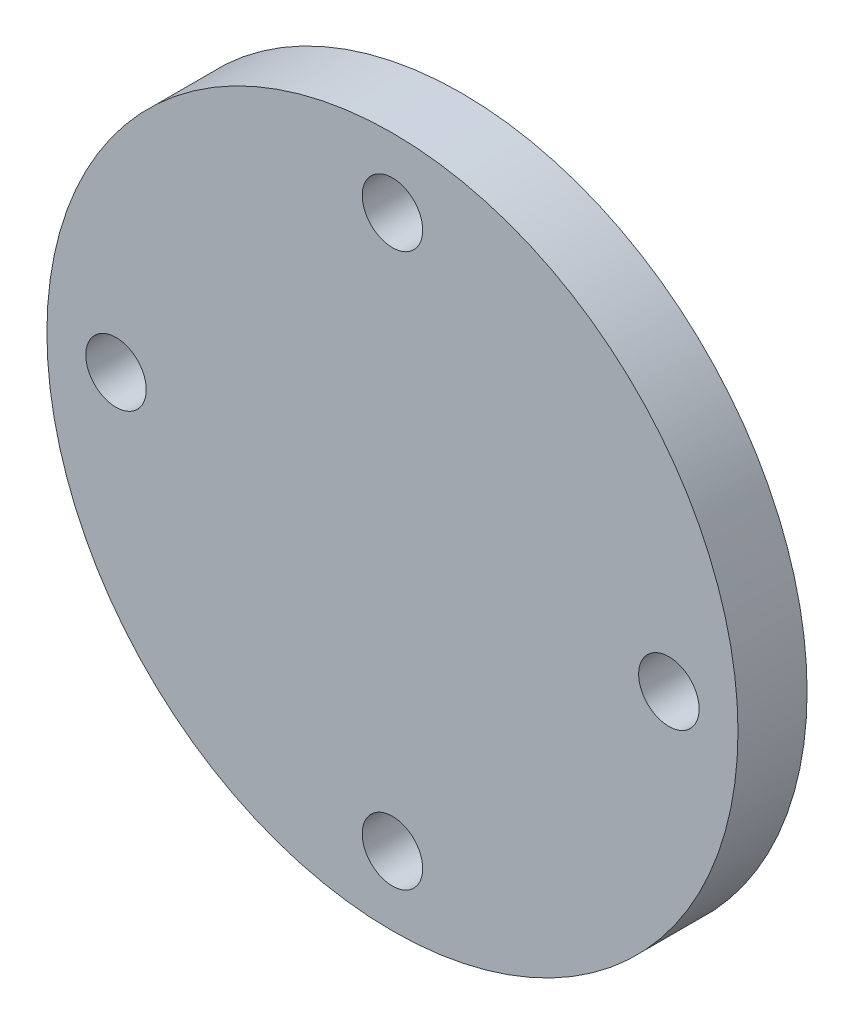
SolidWorks part; units mm, degrees
material "Cast Carbon Steel"
ref_plane "Front Plane" through (0, 0, 0) normal (0, 0, 1) x (1, 0, 0)
ref_plane "Top Plane" through (0, 0, 0) normal (0, 1, 0) x (1, 0, 0)
ref_plane "Right Plane" through (0, 0, 0) normal (1, 0, 0) x (0, 0, -1)
sketch "Sketch1" plane through (0, 0, 0) normal (0, 0, 1) x (1, 0, 0)
  circle A0 centre (0, 0) radius 63.5
  circle A2 centre (-50.8, 0) radius 5.5562
  circle A3 centre (0, 50.8) radius 5.5562
  circle A4 centre (50.8, 0) radius 5.5562
  circle A5 centre (0, -50.8) radius 5.5562
  point P15 (0, 0)
  dimension "D1" = 127
  dimension "D2" = 50.8
  dimension "D3" = 11.1125
  dimension "D4" = 4
extrude "Boss-Extrude1" add sketch "Sketch1" along normal blind 12.7
sketch "Sketch2" plane through (0, 0, 0) normal (0, 0, -1) x (-1, 0, 0)
  line L3 (-2.3876, 7.5699) -> (-2.3876, 5.0638)
  line L4 (-2.3876, 5.0638) -> (2.3876, 5.0638)
  line L5 (2.3876, 5.0638) -> (2.3876, 7.5699)
  circle A0 centre (0, 0) radius 12.7
  arc A1 (-2.3876, 7.5699) -> (2.3876, 7.5699) centre (0, 0) ccw
  dimension "D1" = 25.4
  dimension "D2" = 15.875
  dimension "D3" = 2.5061
  dimension "D4" = 4.7752
  dimension "D5" = 2.5061
extrude "Boss-Extrude2" add sketch "Sketch2" along normal blind 35.56
